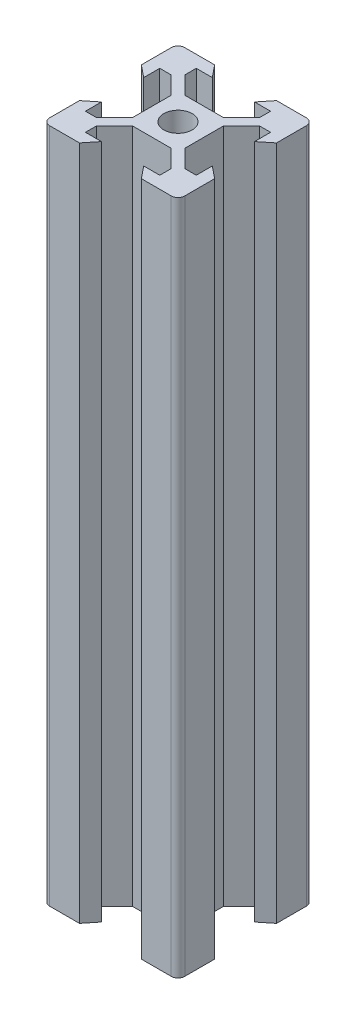
SolidWorks part; units mm, degrees
ref_plane "Front Plane" through (0, 0, 0) normal (0, 0, 1) x (1, 0, 0)
ref_plane "Top Plane" through (0, 0, 0) normal (0, 1, 0) x (1, 0, 0)
ref_plane "Right Plane" through (0, 0, 0) normal (1, 0, 0) x (0, 0, -1)
sketch "Sketch1" plane through (0, 0, 0) normal (0, 1, 0) x (1, 0, 0)
  line L0 (-3.125, 8.2) -> (-4.58, 10)
  line L1 (-9, 10) -> (9, 10)
  line L2 (-10, 9) -> (-10, -9)
  line L3 (-9, -10) -> (9, -10)
  line L4 (10, 9) -> (10, -9)
  line L5 (-10, 10) -> (10, -10) construction
  line L6 (-10, -10) -> (10, 10) construction
  line L7 (-10, 0) -> (0, 0) construction
  line L8 (0, 10) -> (0, 0) construction
  line L9 (-8.2, 3.125) -> (-10, 4.58)
  line L10 (-8.2, 3.125) -> (-8.2, 5.5)
  line L11 (-3.125, 8.2) -> (-5.5, 8.2)
  line L12 (-5.5, 8.2) -> (-5.5, 6.56)
  line L13 (-2.84, 3.9) -> (2.84, 3.9)
  line L14 (-5.5, 6.56) -> (-2.84, 3.9)
  line L15 (-8.2, 5.5) -> (-6.56, 5.5)
  line L16 (-6.56, 5.5) -> (-3.9, 2.84)
  line L17 (-3.9, 2.84) -> (-3.9, -2.84)
  line L18 (3.9, 2.84) -> (3.9, -2.84)
  line L19 (6.56, 5.5) -> (3.9, 2.84)
  line L20 (8.2, 5.5) -> (6.56, 5.5)
  line L21 (8.2, 3.125) -> (8.2, 5.5)
  line L22 (8.2, 3.125) -> (10, 4.58)
  line L23 (3.125, 8.2) -> (4.58, 10)
  line L24 (3.125, 8.2) -> (5.5, 8.2)
  line L25 (5.5, 8.2) -> (5.5, 6.56)
  line L26 (5.5, 6.56) -> (2.84, 3.9)
  line L27 (-8.2, -3.125) -> (-10, -4.58)
  line L28 (-8.2, -3.125) -> (-8.2, -5.5)
  line L29 (-8.2, -5.5) -> (-6.56, -5.5)
  line L30 (-6.56, -5.5) -> (-3.9, -2.84)
  line L31 (8.2, -3.125) -> (10, -4.58)
  line L32 (8.2, -3.125) -> (8.2, -5.5)
  line L33 (8.2, -5.5) -> (6.56, -5.5)
  line L34 (6.56, -5.5) -> (3.9, -2.84)
  line L35 (5.5, -6.56) -> (2.84, -3.9)
  line L36 (5.5, -8.2) -> (5.5, -6.56)
  line L37 (3.125, -8.2) -> (5.5, -8.2)
  line L38 (3.125, -8.2) -> (4.58, -10)
  line L39 (-5.5, -6.56) -> (-2.84, -3.9)
  line L40 (-2.84, -3.9) -> (2.84, -3.9)
  line L41 (-5.5, -8.2) -> (-5.5, -6.56)
  line L42 (-3.125, -8.2) -> (-5.5, -8.2)
  line L43 (-3.125, -8.2) -> (-4.58, -10)
  circle A0 centre (0, 0) radius 2.1
  arc A1 (-10, -9) -> (-9, -10) centre (-9, -9) ccw
  arc A2 (9, -10) -> (10, -9) centre (9, -9) ccw
  arc A3 (9, 10) -> (10, 9) centre (9, 9) cw
  arc A4 (-9, 10) -> (-10, 9) centre (-9, 9) ccw
  point P0 (0, 0)
  point P10 (-3.2, 7.8844)
  point P11 (-3.2, 8.9154)
  point P35 (0, 3.9)
  point P40 (-3.9, 0)
  point P41 (3.9, 0)
  dimension "D3" = 4.2
  dimension "D2" = 1
  dimension "D1" = 20
  dimension "D4" = 6.1
  dimension "D5" = 6.25
  dimension "D6" = 11
  dimension "D7" = 5.68
  dimension "D8" = 9.16
  dimension "D9" = 1.8
extrude "Boss-Extrude1" add sketch "Sketch1" along normal blind 100 contours L43 L42 L41 L39 L40 L35 L36 L37 L38 L3 L4 L31 L32 L33 L34 L18 L19 L20 L21 L22 L1 L23 L24 L25 L26 L13 L14 L12 L11 L0 L2 L9 L10 L15 L16 L17 L30 L29 L28 L27 A0
